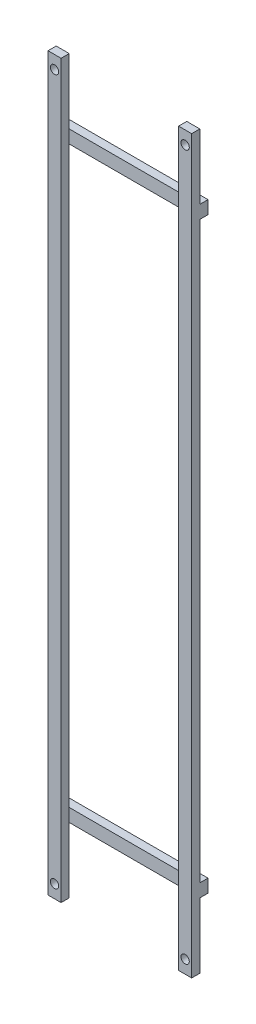
SolidWorks part; units mm, degrees
ref_plane "Front Plane" through (0, 0, 0) normal (0, 0, 1) x (1, 0, 0)
ref_plane "Top Plane" through (0, 0, 0) normal (0, 1, 0) x (1, 0, 0)
ref_plane "Right Plane" through (0, 0, 0) normal (1, 0, 0) x (0, 0, -1)
ref_plane "Plane1" through (45, 0, 0) normal (-1, 0, 0) x (0, -1, 0)
sketch "Sketch1" plane through (45, 0, 0) normal (-1, 0, 0) x (0, -1, 0)
  line L0 (-37.6165, 80) -> (-37.6165, 0)
  line L1 (-37.6165, 0) -> (472.3835, 0)
  line L2 (472.3835, 0) -> (472.3835, 80)
  line L3 (472.3835, 80) -> (-37.6165, 80)
  dimension "D1" = 510
extrude "Boss-Extrude1" add sketch "Sketch1" against normal blind 10
sketch "Sketch2" plane through (45, 0, 0) normal (-1, 0, 0) x (0, 0, 1)
  line L0 (0, -22.3835) -> (0, -412.3835)
  line L1 (0, -412.3835) -> (70, -412.3835)
  line L2 (70, -412.3835) -> (70, -22.3835)
  line L3 (70, -22.3835) -> (0, -22.3835)
extrude "Cut-Extrude1" cut sketch "Sketch2" against normal through all
sketch "Sketch3" plane through (45, 0, 0) normal (-1, 0, 0) x (0, 0, 1)
  line L0 (0, -12.3835) -> (70, -12.3835)
  line L1 (70, -12.3835) -> (70, 37.6165)
  line L2 (70, 37.6165) -> (0, 37.6165)
  line L3 (0, 37.6165) -> (0, -12.3835)
extrude "Cut-Extrude2" cut sketch "Sketch3" against normal through all
sketch "Sketch4" plane through (45, 0, 0) normal (-1, 0, 0) x (0, 0, 1)
  line L0 (70, -22.3835) -> (0, -22.3835)
  line L1 (0, -22.3835) -> (0, -12.3835)
  line L2 (0, -12.3835) -> (70, -12.3835)
  line L3 (70, -12.3835) -> (70, -22.3835)
extrude "Boss-Extrude2" add sketch "Sketch4" along normal blind 100
sketch "Sketch5" plane through (45, 0, 0) normal (-1, 0, 0) x (0, 0, 1)
  line L0 (70, -472.3835) -> (70, -422.3835)
  line L1 (70, -422.3835) -> (0, -422.3835)
  line L2 (0, -422.3835) -> (0, -472.3835)
  line L3 (0, -472.3835) -> (70, -472.3835)
extrude "Cut-Extrude3" cut sketch "Sketch5" against normal through all
sketch "Sketch6" plane through (45, 0, 0) normal (-1, 0, 0) x (0, 0, 1)
  line L0 (70, -422.3835) -> (0, -422.3835)
  line L1 (0, -422.3835) -> (0, -412.3835)
  line L2 (0, -412.3835) -> (70, -412.3835)
  line L3 (70, -412.3835) -> (70, -422.3835)
extrude "Boss-Extrude3" add sketch "Sketch6" along normal blind 100
sketch "Sketch7" plane through (0, 0, 70) normal (0, 0, 1) x (1, 0, 0)
  line L0 (-45, -12.3835) -> (-45, -472.3835)
  line L1 (-45, -472.3835) -> (-55, -472.3835)
  line L2 (-55, -472.3835) -> (-55, -12.3835)
  line L3 (-55, -12.3835) -> (-45, -12.3835)
extrude "Boss-Extrude4" add sketch "Sketch7" along normal blind 10
sketch "Sketch8" plane through (0, -12.3835, 0) normal (0, 1, 0) x (-1, 0, 0)
  line L0 (55, 80) -> (55, 70)
  line L1 (55, 70) -> (45, 70)
  line L2 (45, 70) -> (45, 80)
  line L3 (45, 80) -> (55, 80)
extrude "Boss-Extrude5" add sketch "Sketch8" along normal blind 50
sketch "Sketch9" plane through (0, -22.3835, 0) normal (0, -1, 0) x (1, 0, 0)
  line L0 (45, 0) -> (45, 60)
  line L1 (45, 60) -> (-45, 60)
  line L2 (-45, 60) -> (-45, 0)
  line L3 (-45, 0) -> (45, 0)
extrude "Cut-Extrude4" cut sketch "Sketch9" against normal through all
sketch "Sketch10" plane through (0, -412.3835, 0) normal (0, 1, 0) x (-1, 0, 0)
  line L0 (45, 0) -> (45, 60)
  line L1 (45, 60) -> (-45, 60)
  line L2 (-45, 60) -> (-45, 0)
  line L3 (-45, 0) -> (45, 0)
extrude "Cut-Extrude5" cut sketch "Sketch10" against normal through all
hole_wizard "Hole1" positions "Sketch12" profile "Sketch11" legacy
sketch "Sketch12" plane through (0, 0, 70) normal (0, 0, -1) x (-1, 0, 0)
  point P0 (-50, 27.6165)
  point P1 (50, -462.3835)
sketch "Sketch11" plane through (50, 27.6165, 70) normal (1, 0, 0) x (0, 1, 0)
  line L0 (0, 0) -> (0, 10)
  line L1 (0, 10) -> (3.175, 10)
  line L2 (3.175, 10) -> (3.175, 0)
  line L3 (3.175, 0) -> (0, 0)
  line L4 (0, 110) -> (0, -10) construction
  dimension "Diameter" = 6.35
  dimension "Depth" = 10
hole_wizard "Hole2" positions "Sketch14" profile "Sketch13" legacy
sketch "Sketch14" plane through (0, 0, 80) normal (0, 0, 1) x (1, 0, 0)
  point P0 (50, -462.3835)
  point P1 (-50, 27.6165)
sketch "Sketch13" plane through (50, -462.3835, 80) normal (1, 0, 0) x (0, -1, 0)
  line L0 (0, 0) -> (0, 80)
  line L1 (0, 80) -> (3.175, 80)
  line L2 (3.175, 80) -> (3.175, 0)
  line L3 (3.175, 0) -> (0, 0)
  line L4 (0, 110) -> (0, -10) construction
  dimension "Diameter" = 6.35
  dimension "Depth" = 80
scale "Scale1" scale about centroid uniform scaling yes scale factor 4
sketch "Sketch16" plane through (220, 0, 0) normal (1, 0, 0) x (0, 0, -1)
  line L2 (-81.5788, -1237.3835) -> (-81.5788, -1037.3835) construction
  line L3 (363.7757, 866.3876) -> (-56.5788, 866.3876)
  line L4 (363.7757, 866.3876) -> (363.7757, -1181.0534)
  line L5 (363.7757, -1181.0534) -> (-56.5788, -1181.0534)
  line L6 (-56.5788, 866.3876) -> (-56.5788, -1181.0534)
  line L8 (-81.5788, -997.3835) -> (-81.5788, 562.6165) construction
  line L9 (-610.8485, 823.0413) -> (-106.5788, 823.0413)
  line L10 (-610.8485, 823.0413) -> (-610.8485, -1320.8418)
  line L11 (-610.8485, -1320.8418) -> (-106.5788, -1320.8418)
  line L12 (-106.5788, 823.0413) -> (-106.5788, -1320.8418)
  dimension "D1" = 25
  dimension "D2" = 25
extrude "Cut-Extrude6" cut sketch "Sketch16" against normal blind 600
sketch "Sketch17" plane through (0, 0, 106.5788) normal (0, 0, 1) x (1, 0, 0)
  line L0 (-220, -1237.3835) -> (-220, 802.6165) construction
  line L1 (-220, -217.3835) -> (486.7471, -217.3835)
  line L2 (-220, -217.3835) -> (-220, 873.5026)
  line L3 (-220, 873.5026) -> (486.7471, 873.5026)
  line L4 (486.7471, -217.3835) -> (486.7471, 873.5026)
extrude "Cut-Extrude7" cut sketch "Sketch17" against normal blind 100
sketch "Sketch18" plane through (0, -217.3835, 0) normal (0, 1, 0) x (1, 0, 0)
  line L1 (-220, -81.5788) -> (-180, -81.5788)
  line L2 (-220, -81.5788) -> (-220, -106.5788)
  line L3 (-220, -106.5788) -> (-180, -106.5788)
  line L4 (-180, -81.5788) -> (-180, -106.5788)
  line L5 (180, -81.5788) -> (220, -81.5788)
  line L6 (180, -81.5788) -> (180, -106.5788)
  line L7 (180, -106.5788) -> (220, -106.5788)
  line L8 (220, -81.5788) -> (220, -106.5788)
extrude "Boss-Extrude6" add sketch "Sketch18" along normal blind 1
sketch "Sketch20" plane through (0, 0, 106.5788) normal (0, 0, 1) x (1, 0, 0)
  line L0 (-391.2787, -216.3835) -> (585.6528, -216.3835) construction
  line L1 (-220, -216.3835) -> (-180, -216.3835)
  line L2 (-220, 1002.6165) -> (-220, -216.3835)
  line L4 (-180, 1002.6165) -> (-180, -216.3835)
  line L5 (180, -216.3835) -> (220, -216.3835)
  line L6 (180, 1002.6165) -> (180, -216.3835)
  line L8 (220, 1002.6165) -> (220, -216.3835)
  line L9 (180, 1002.6165) -> (220, 1002.6165)
  line L10 (-220, 1002.6165) -> (-180, 1002.6165)
  circle A2 centre (200, 962.6165) radius 12.7
  circle A3 centre (-200, 962.6165) radius 12.7
extrude "Boss-Extrude9" add sketch "Sketch20" against normal blind 25
sketch "Sketch21" plane through (0, 0, 81.5788) normal (0, 0, -1) x (-1, 0, 0)
  line L1 (-389.8468, -117.3835) -> (638.2169, -117.3835) construction
  line L2 (220, 762.6165) -> (220, 802.6165)
  line L7 (-220, 802.6165) -> (220, 802.6165)
  line L8 (-220, 762.6165) -> (-220, 802.6165)
  line L9 (-220, 762.6165) -> (220, 762.6165)
extrude "Boss-Extrude10" add sketch "Sketch21" along normal blind 25
